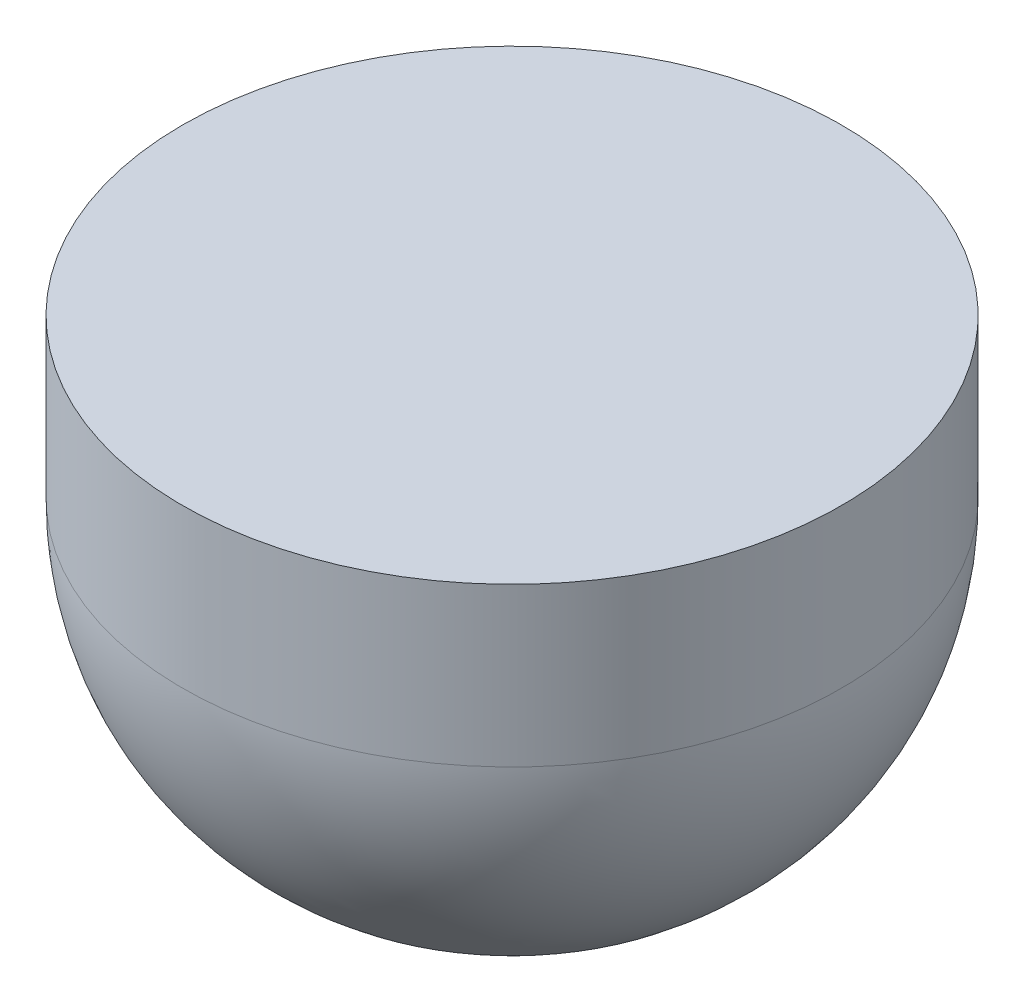
SolidWorks part; units mm, degrees
ref_plane "Front Plane" through (0, 0, 0) normal (0, 0, 1) x (1, 0, 0)
ref_plane "Top Plane" through (0, 0, 0) normal (0, 1, 0) x (1, 0, 0)
ref_plane "Right Plane" through (0, 0, 0) normal (1, 0, 0) x (0, 0, -1)
sketch "Sketch2" plane through (0, 0, 0) normal (0, 0, 1) x (1, 0, 0)
  line L0 (-12.5, 0) -> (0, 0)
  line L1 (0, 0) -> (0, -18) construction
  line L2 (-12.5, 0) -> (-12.5, -6)
  line L3 (-0.5, -18) -> (0, -18)
  line L4 (0, 0) -> (0, -18)
  arc A0 (-12.5, -6) -> (-0.5, -18) centre (-0.5, -6) ccw
  dimension "D1" = 12
  dimension "D2" = 18
revolve "Revolve1" add sketch "Sketch2" angle 360 about L1
